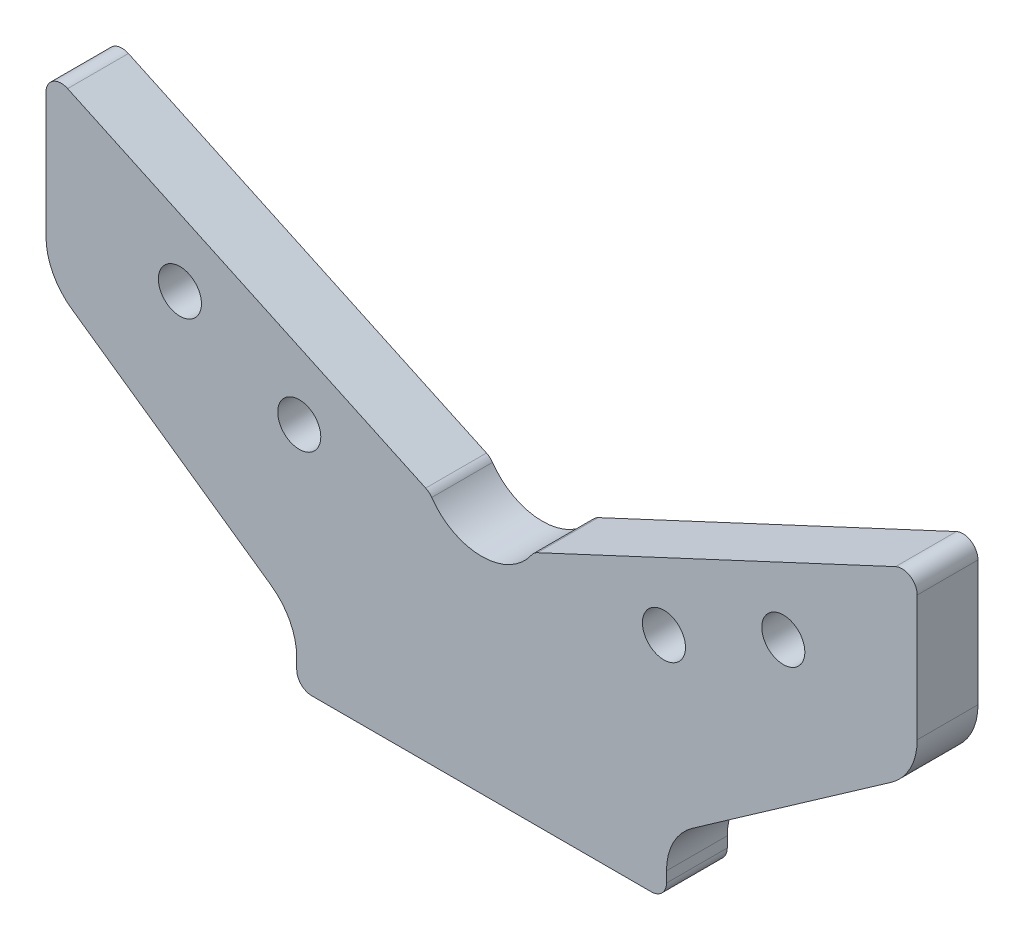
SolidWorks part; units mm, degrees
ref_plane "Front" through (0, 0, 0) normal (0, 0, 1) x (1, 0, 0)
ref_plane "Top" through (0, 0, 0) normal (0, 1, 0) x (1, 0, 0)
ref_plane "Right" through (0, 0, 0) normal (1, 0, 0) x (0, 0, -1)
sketch "Sketch1" plane through (0, 0, 0) normal (0, 0, 1) x (1, 0, 0)
  line L0 (36.5, 3) -> (36.5, 5.0929)
  line L1 (-36.5, 3) -> (-36.5, 5.0929)
  line L2 (0, 0) -> (33.5, 0)
  line L3 (0, 0) -> (-33.5, 0)
  line L4 (81.7321, 79.7189) -> (11.0434, 46.7562)
  line L5 (0, 0) -> (0, 41.6066) construction
  line L6 (-86, 52.2468) -> (-86, 77)
  line L7 (-81.7321, 79.7189) -> (-11.0434, 46.7562)
  line L8 (41.6171, 14.9227) -> (80.8829, 42.417)
  line L10 (86, 52.2468) -> (86, 77)
  line L11 (-41.6171, 14.9227) -> (-80.8829, 42.417)
  arc A0 (41.6171, 14.9227) -> (36.5, 5.0929) centre (48.5, 5.0929) ccw
  arc A1 (-36.5, 5.0929) -> (-41.6171, 14.9227) centre (-48.5, 5.0929) ccw
  arc A2 (33.5, 0) -> (36.5, 3) centre (33.5, 3) ccw
  arc A3 (81.7321, 79.7189) -> (86, 77) centre (83, 77) cw
  arc A4 (-86, 77) -> (-81.7321, 79.7189) centre (-83, 77) cw
  arc A5 (80.8829, 42.417) -> (86, 52.2468) centre (74, 52.2468) ccw
  arc A6 (-36.5, 3) -> (-33.5, 0) centre (-33.5, 3) ccw
  arc A9 (-80.8829, 42.417) -> (-86, 52.2468) centre (-74, 52.2468) cw
  arc A10 (-9.849, 45.7512) -> (9.849, 45.7512) centre (0, 52.6066) ccw
  arc A11 (-9.849, 45.7512) -> (-11.0434, 46.7562) centre (-12.3113, 44.0373) ccw
  arc A12 (9.849, 45.7512) -> (11.0434, 46.7562) centre (12.3113, 44.0373) cw
  point P3 (36.5, 11.3397)
  point P10 (-36.5, 11.3397)
  point P14 (36.5, 0)
  point P19 (86, 81.7091)
  point P23 (-86, 81.7091)
  point P26 (86, 0)
  point P29 (-36.5, 0)
  point P32 (86, 46)
  point P43 (0, 41.6066)
  dimension "D5" = 34
  dimension "D6" = 3
  dimension "D7" = 12
  dimension "D8" = 3
  dimension "D13" = 12
  dimension "D15" = 12
  dimension "D16" = 3
  dimension "D2" = 73
  dimension "D3" = 65
  dimension "D4" = 25
  dimension "D9" = 172
  dimension "D10" = 80
  dimension "D11" = 55
  dimension "D12" = 41.6066
  dimension "D14" = 11
extrude "Extrude1" add sketch "Sketch1" along normal blind 12
hole_wizard "M10 gevindhuller" positions "Sketch5" profile "Sketch4" legacy
sketch "Sketch5" plane through (0, 0, 12) normal (0, 0, 1) x (1, 0, 0)
  line L0 (0, 0) -> (0, 52.6066) construction
  line L1 (-36, 45.1531) -> (-59.564, 56.1412) construction
  line L2 (-11.0434, 46.7562) -> (-81.7321, 79.7189) construction
  point P0 (-59.564, 56.1412)
  point P6 (-36, 45.1531)
  point P10 (59.564, 56.1412)
  point P11 (36, 45.1531)
  dimension "D1" = 12
  dimension "D2" = 26
  dimension "D3" = 72
sketch "Sketch4" plane through (-59.564, 56.1412, 12) normal (1, 0, 0) x (0, -1, 0)
  line L0 (0, 0) -> (0, 24.5537)
  line L1 (0, 24.5537) -> (4.25, 22)
  line L2 (4.25, 22) -> (4.25, 0)
  line L4 (4.25, 0) -> (0, 0)
  line L6 (0, 24.5537) -> (-4.25, 22) construction
  line L7 (0, -4.2442) -> (0, 117.3081) construction
  dimension "Diameter" = 8.5
  dimension "Depth" = 22
  dimension "Drill Angle" = 118
cosmetic thread "Cosmetic Thread1" parameters "D1"=17, "D2"=10
cosmetic thread "Cosmetic Thread2" parameters "D1"=17, "D2"=10
cosmetic thread "Cosmetic Thread3" parameters "D1"=17, "D2"=10
cosmetic thread "Cosmetic Thread4" parameters "D1"=17, "D2"=10
